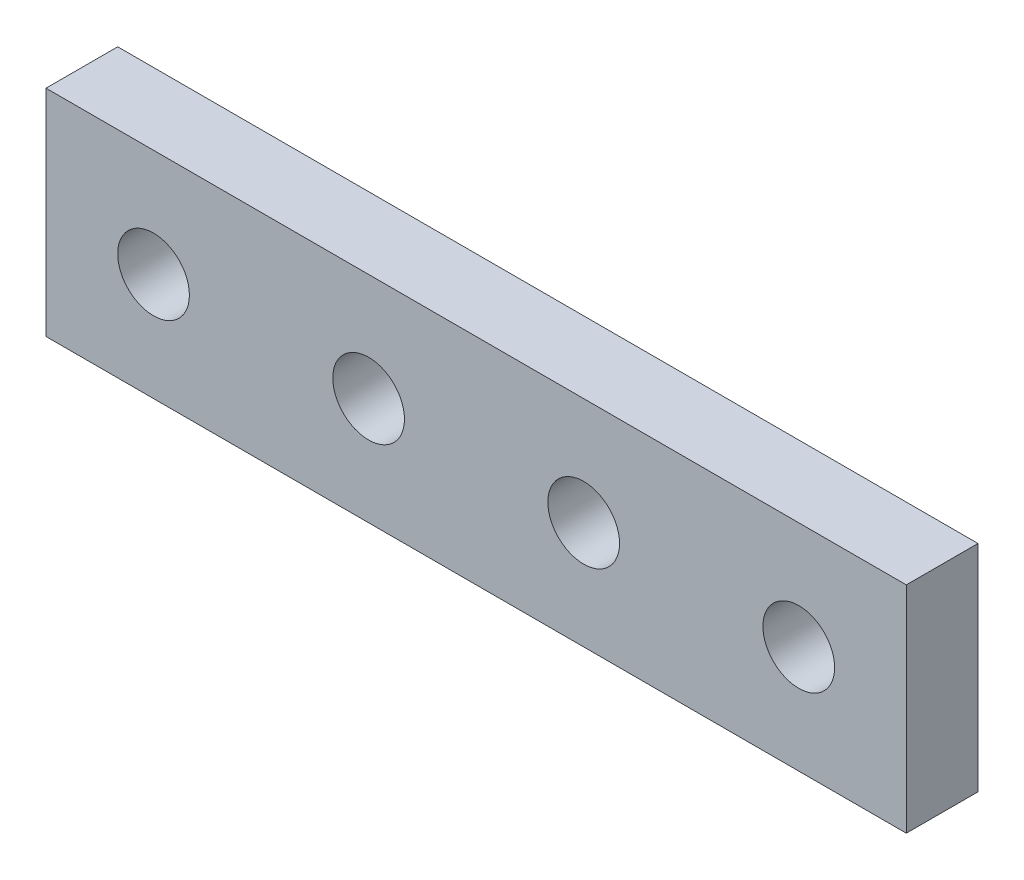
SolidWorks part; units mm, degrees
ref_plane "Front Plane" through (0, 0, 0) normal (0, 0, 1) x (1, 0, 0)
ref_plane "Top Plane" through (0, 0, 0) normal (0, 1, 0) x (1, 0, 0)
ref_plane "Right Plane" through (0, 0, 0) normal (1, 0, 0) x (0, 0, -1)
sketch "Sketch1" plane through (0, 0, 0) normal (0, 0, 1) x (1, 0, 0)
  line L0 (15, 15) -> (45, 15) construction
  line L1 (0, 0) -> (120, 0)
  line L2 (0, 0) -> (0, 30)
  line L3 (0, 30) -> (120, 30)
  line L4 (120, 0) -> (120, 30)
  circle A0 centre (15, 15) radius 5
  circle A1 centre (45, 15) radius 5
  circle A2 centre (75, 15) radius 5
  circle A3 centre (105, 15) radius 5
  dimension "D3" = 10
  dimension "D1" = 120
  dimension "D2" = 30
  dimension "D4" = 15
  dimension "D5" = 15
  dimension "D7" = 30
  dimension "D6" = 4
extrude "Boss-Extrude1" add sketch "Sketch1" along normal blind 10
